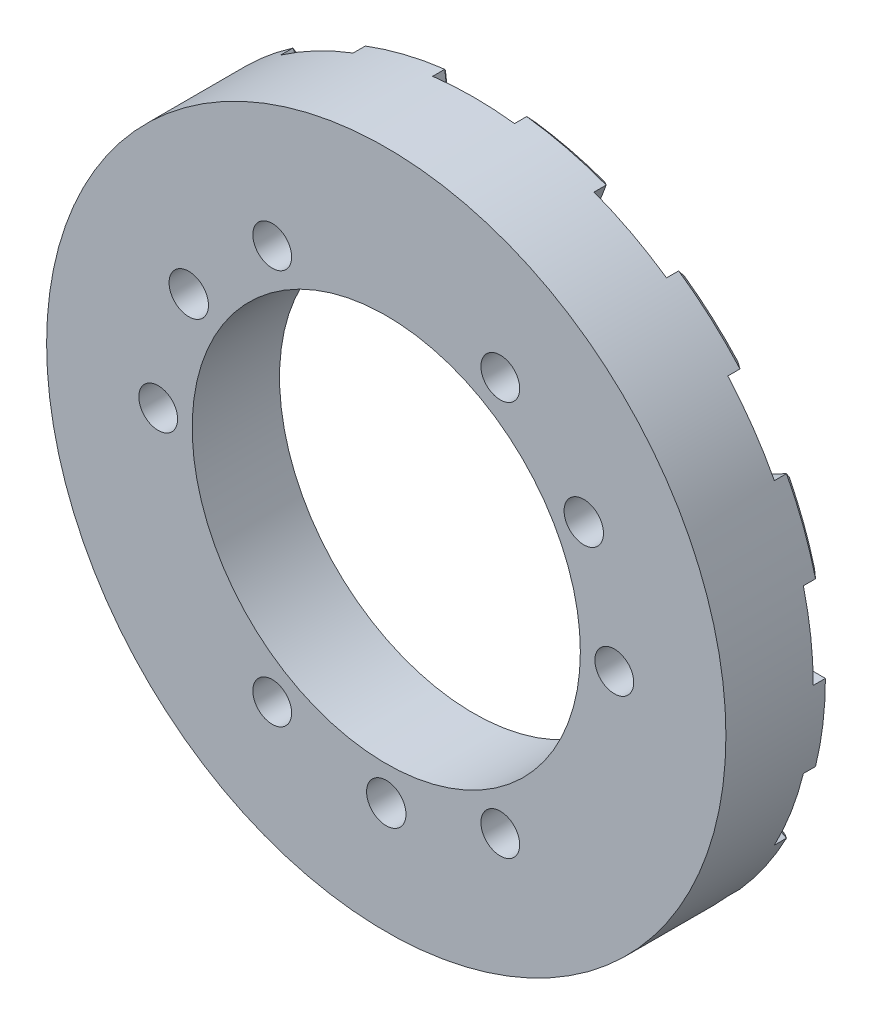
SolidWorks part; units mm, degrees
ref_plane "前视基准面" through (0, 0, 0) normal (0, 0, 1) x (1, 0, 0)
ref_plane "上视基准面" through (0, 0, 0) normal (0, 1, 0) x (1, 0, 0)
ref_plane "右视基准面" through (0, 0, 0) normal (1, 0, 0) x (0, 0, -1)
sketch "草图1" plane through (0, 0, 0) normal (0, 0, 1) x (1, 0, 0)
  circle A0 centre (0, 0) radius 70
  circle A1 centre (0, 0) radius 40
  dimension "D1" = 140
  dimension "D2" = 80
extrude "凸台-拉伸1" add sketch "草图1" along normal blind 18
sketch "草图2" plane through (0, 0, 18) normal (0, 0, 1) x (1, 0, 0)
  circle A0 centre (47, 0) radius 4
  dimension "D1" = 8
  dimension "D2" = 47
extrude "切除-拉伸1" cut sketch "草图2" against normal blind 20
pattern_circular "阵列(圆周)1" count 6 over 360 about axis through (0, 0, 0) along (0, 0, 1) of "切除-拉伸1"
sketch "草图3" plane through (0, 0, 18) normal (0, 0, 1) x (1, 0, 0)
  line L0 (40.7032, 23.5) -> (0, 0) construction
  line L1 (0, 0) -> (47, 0) construction
  circle A0 centre (0, 0) radius 47 construction
  circle A1 centre (40.7032, 23.5) radius 4.06
  dimension "D2" = 8.12
  dimension "D1" = 30
extrude "切除-拉伸2" cut sketch "草图3" against normal blind 20
pattern_circular "阵列(圆周)2" count 3 over 360 about axis through (0, 0, 0) along (0, 0, 1) of "切除-拉伸2"
sketch "草图4" plane through (0, 0, 0) normal (0, 0, -1) x (-1, 0, 0)
  line L0 (60, 0) -> (70, 0)
  line L1 (58.2565, 14.3589) -> (67.9659, 16.7521)
  line L2 (53.1274, 27.8834) -> (61.9819, 32.5306)
  line L3 (44.9106, 39.7874) -> (52.3958, 46.4186)
  line L4 (34.0839, 49.379) -> (39.7645, 57.6089)
  line L5 (21.2763, 56.101) -> (24.8223, 65.4511)
  line L6 (7.2322, 59.5625) -> (8.4376, 69.4896)
  line L7 (-7.2322, 59.5625) -> (-8.4376, 69.4896)
  line L8 (-21.2763, 56.101) -> (-24.8223, 65.4511)
  line L9 (-34.0839, 49.379) -> (-39.7645, 57.6089)
  line L10 (-44.9106, 39.7874) -> (-52.3958, 46.4186)
  line L11 (-53.1274, 27.8834) -> (-61.9819, 32.5306)
  line L12 (-58.2565, 14.3589) -> (-67.9659, 16.7521)
  line L13 (-60, 0) -> (-70, 0)
  line L14 (-58.2565, -14.3589) -> (-67.9659, -16.7521)
  line L15 (-53.1274, -27.8834) -> (-61.9819, -32.5306)
  line L16 (-44.9106, -39.7874) -> (-52.3958, -46.4186)
  line L17 (-34.0839, -49.379) -> (-39.7645, -57.6089)
  line L18 (-21.2763, -56.101) -> (-24.8223, -65.4511)
  line L19 (-7.2322, -59.5625) -> (-8.4376, -69.4896)
  line L20 (7.2322, -59.5625) -> (8.4376, -69.4896)
  line L21 (21.2763, -56.101) -> (24.8223, -65.4511)
  line L22 (34.0839, -49.379) -> (39.7645, -57.6089)
  line L23 (44.9106, -39.7874) -> (52.3958, -46.4186)
  line L24 (53.1274, -27.8834) -> (61.9819, -32.5306)
  line L25 (58.2565, -14.3589) -> (67.9659, -16.7521)
  arc A0 (58.2565, 14.3589) -> (53.1274, 27.8834) centre (0, 0) ccw
  circle A1 centre (0, 0) radius 70 construction
  arc A2 (67.9659, 16.7521) -> (61.9819, 32.5306) centre (0, 0) ccw
  arc A3 (52.3958, 46.4186) -> (39.7645, 57.6089) centre (0, 0) ccw
  arc A4 (44.9106, 39.7874) -> (34.0839, 49.379) centre (0, 0) ccw
  arc A5 (24.8223, 65.4511) -> (8.4376, 69.4896) centre (0, 0) ccw
  arc A6 (21.2763, 56.101) -> (7.2322, 59.5625) centre (0, 0) ccw
  arc A7 (-8.4376, 69.4896) -> (-24.8223, 65.4511) centre (0, 0) ccw
  arc A8 (-7.2322, 59.5625) -> (-21.2763, 56.101) centre (0, 0) ccw
  arc A9 (-39.7645, 57.6089) -> (-52.3958, 46.4186) centre (0, 0) ccw
  arc A10 (-34.0839, 49.379) -> (-44.9106, 39.7874) centre (0, 0) ccw
  arc A11 (-61.9819, 32.5306) -> (-67.9659, 16.7521) centre (0, 0) ccw
  arc A12 (-53.1274, 27.8834) -> (-58.2565, 14.3589) centre (0, 0) ccw
  arc A13 (-70, 0) -> (-67.9659, -16.7521) centre (0, 0) ccw
  arc A14 (-60, 0) -> (-58.2565, -14.3589) centre (0, 0) ccw
  arc A15 (-53.1274, -27.8834) -> (-44.9106, -39.7874) centre (0, 0) ccw
  arc A16 (-61.9819, -32.5306) -> (-52.3958, -46.4186) centre (0, 0) ccw
  arc A17 (-34.0839, -49.379) -> (-21.2763, -56.101) centre (0, 0) ccw
  arc A18 (-39.7645, -57.6089) -> (-24.8223, -65.4511) centre (0, 0) ccw
  arc A19 (-7.2322, -59.5625) -> (7.2322, -59.5625) centre (0, 0) ccw
  arc A20 (-8.4376, -69.4896) -> (8.4376, -69.4896) centre (0, 0) ccw
  arc A21 (24.8223, -65.4511) -> (39.7645, -57.6089) centre (0, 0) ccw
  arc A22 (21.2763, -56.101) -> (34.0839, -49.379) centre (0, 0) ccw
  arc A23 (44.9106, -39.7874) -> (53.1274, -27.8834) centre (0, 0) ccw
  arc A24 (52.3958, -46.4186) -> (61.9819, -32.5306) centre (0, 0) ccw
  arc A25 (67.9659, -16.7521) -> (70, 0) centre (0, 0) ccw
  arc A26 (58.2565, -14.3589) -> (60, 0) centre (0, 0) ccw
  dimension "D1" = 120
extrude "凸台-拉伸2" add sketch "草图4" along normal blind 3.5
chamfer "倒角1" distance 1 angle 45 52 edges at (-23.0493, -60.7761, -3.5) (-27.8834, -53.1274, -3.5) (-36.9242, -53.494, -3.5) (-32.5306, -61.9819, -3.5) (7.8349, -64.5261, -3.5) (0, -60, -3.5) (-7.8349, -64.5261, -3.5) (0, -70, -3.5) (36.9242, -53.494, -3.5) (27.8834, -53.1274, -3.5) (23.0493, -60.7761, -3.5) (32.5306, -61.9819, -3.5) (57.5546, -30.207, -3.5) (49.379, -34.0839, -3.5) (48.6532, -43.103, -3.5) (57.6089, -39.7645, -3.5) (65, 0, -3.5) (59.5625, -7.2322, -3.5) (63.1112, -15.5555, -3.5) (69.4896, -8.4376, -3.5) (57.5546, 30.207, -3.5) (56.101, 21.2763, -3.5) (63.1112, 15.5555, -3.5) (65.4511, 24.8223, -3.5) (36.9242, 53.494, -3.5) (39.7874, 44.9106, -3.5) (48.6532, 43.103, -3.5) (46.4186, 52.3958, -3.5) (7.8349, 64.5261, -3.5) (14.3589, 58.2565, -3.5) (23.0493, 60.7761, -3.5) (16.7521, 67.9659, -3.5) (-23.0493, 60.7761, -3.5) (-14.3589, 58.2565, -3.5) (-7.8349, 64.5261, -3.5) (-16.7521, 67.9659, -3.5) (-48.6532, 43.103, -3.5) (-39.7874, 44.9106, -3.5) (-36.9242, 53.494, -3.5) (-46.4186, 52.3958, -3.5) (-63.1112, 15.5555, -3.5) (-56.101, 21.2763, -3.5) (-57.5546, 30.207, -3.5) (-65.4511, 24.8223, -3.5) (-63.1112, -15.5555, -3.5) (-59.5625, -7.2322, -3.5) (-65, 0, -3.5) (-69.4896, -8.4376, -3.5) (-48.6532, -43.103, -3.5) (-49.379, -34.0839, -3.5) (-57.5546, -30.207, -3.5) (-57.6089, -39.7645, -3.5)
